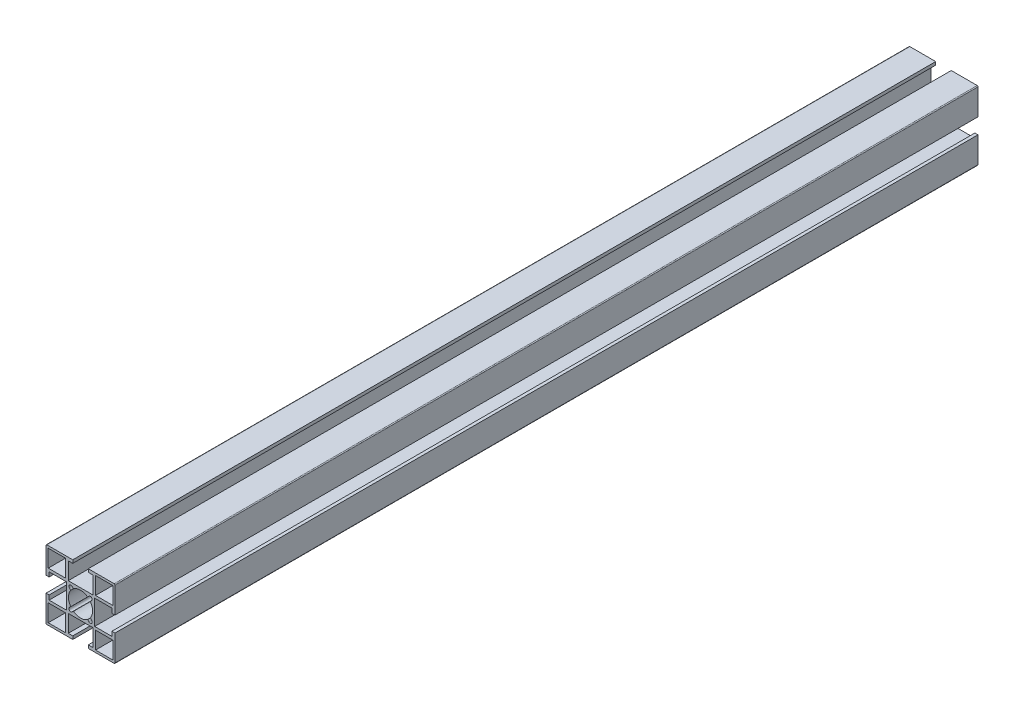
SolidWorks part; units mm, degrees
ref_plane "前视基准面" through (0, 0, 0) normal (0, 0, 1) x (1, 0, 0)
ref_plane "上视基准面" through (0, 0, 0) normal (0, 1, 0) x (1, 0, 0)
ref_plane "右视基准面" through (0, 0, 0) normal (1, 0, 0) x (0, 0, -1)
other "Configuration Table"
sketch "草图1" plane through (0, 0, 0) normal (1, 0, 0) x (0, 0, -1)
  line L0 (0, 0) -> (500, 0)
other "铝型材 40 X 40A X R0.5(1)"
ref_plane "基准面1" through (0, 0, 0) normal (0, 0, -1) x (0, 1, 0)
sketch "Sketch114" plane through (0, 0, 0) normal (0, 0, -1) x (0, 1, 0)
  line L0 (0, 0) -> (0, 16.3773) construction
  line L1 (0, 0) -> (-5.6569, 5.6569) construction
  line L2 (-19.5, 20) -> (-4.5, 20)
  line L3 (-20, 19.5) -> (-20, 4.5)
  line L4 (-19.5, -20) -> (-4.5, -20)
  line L5 (20, 19.5) -> (20, 4.5)
  line L6 (-4.879, 6.4347) -> (-4.1104, 5.6661)
  line L7 (-6.4347, 4.879) -> (-5.6661, 4.1104)
  line L8 (6.4347, 4.879) -> (5.6661, 4.1104)
  line L9 (0, 0) -> (20, 0) construction
  line L10 (4.879, 6.4347) -> (4.1104, 5.6661)
  line L11 (4.879, -6.4347) -> (4.1104, -5.6661)
  line L12 (6.4347, -4.879) -> (5.6661, -4.1104)
  line L13 (-6.4347, -4.879) -> (-5.6661, -4.1104)
  line L14 (-4.879, -6.4347) -> (-4.1104, -5.6661)
  line L15 (-4.5, 20) -> (-4.5, 18.2)
  line L16 (-18.7, 18.7) -> (-8.7, 18.7)
  line L17 (-18.7, 18.7) -> (-18.7, 8.7)
  line L18 (-18.7, 8.7) -> (-8.7, 8.7)
  line L19 (-8.7, 18.7) -> (-8.7, 8.7)
  line L20 (-7.1, 18.2) -> (-4.5, 18.2)
  line L21 (-7.1, 18.2) -> (-7.1, 8.2)
  line L22 (-7.1, 8.2) -> (7.1, 8.2)
  line L23 (7.1, 18.2) -> (7.1, 8.2)
  line L24 (4.5, 20) -> (4.5, 18.2)
  line L25 (4.5, 20) -> (19.5, 20)
  line L26 (4.5, 18.2) -> (7.1, 18.2)
  line L27 (8.7, 18.7) -> (8.7, 8.7)
  line L28 (18.7, 8.7) -> (8.7, 8.7)
  line L29 (18.7, 18.7) -> (18.7, 8.7)
  line L30 (18.7, 18.7) -> (8.7, 18.7)
  line L31 (18.2, 7.1) -> (8.2, 7.1)
  line L32 (18.2, 7.1) -> (18.2, 4.5)
  line L33 (20, 4.5) -> (18.2, 4.5)
  line L34 (8.2, 7.1) -> (8.2, -7.1)
  line L35 (18.2, -7.1) -> (8.2, -7.1)
  line L36 (18.2, -4.5) -> (18.2, -7.1)
  line L37 (20, -4.5) -> (18.2, -4.5)
  line L38 (7.1, -18.2) -> (7.1, -8.2)
  line L39 (7.1, -18.2) -> (4.5, -18.2)
  line L40 (4.5, -20) -> (4.5, -18.2)
  line L41 (7.1, -8.2) -> (-7.1, -8.2)
  line L42 (-7.1, -18.2) -> (-7.1, -8.2)
  line L43 (-4.5, -18.2) -> (-7.1, -18.2)
  line L44 (-4.5, -20) -> (-4.5, -18.2)
  line L45 (-18.2, -7.1) -> (-8.2, -7.1)
  line L46 (-18.2, -7.1) -> (-18.2, -4.5)
  line L47 (-20, -4.5) -> (-18.2, -4.5)
  line L48 (-8.2, -7.1) -> (-8.2, 7.1)
  line L49 (-18.2, 7.1) -> (-8.2, 7.1)
  line L50 (-18.2, 4.5) -> (-18.2, 7.1)
  line L51 (-20, 4.5) -> (-18.2, 4.5)
  line L52 (4.5, -20) -> (19.5, -20)
  line L53 (-20, -4.5) -> (-20, -19.5)
  line L54 (20, -4.5) -> (20, -19.5)
  line L55 (18.7, -18.7) -> (18.7, -8.7)
  line L56 (18.7, -8.7) -> (8.7, -8.7)
  line L57 (8.7, -18.7) -> (8.7, -8.7)
  line L58 (18.7, -18.7) -> (8.7, -18.7)
  line L59 (-8.7, -18.7) -> (-8.7, -8.7)
  line L60 (-18.7, -8.7) -> (-8.7, -8.7)
  line L61 (-18.7, -18.7) -> (-8.7, -18.7)
  line L62 (-18.7, -18.7) -> (-18.7, -8.7)
  arc A0 (-4.1104, 5.6661) -> (4.1104, 5.6661) centre (0, 0) cw
  arc A1 (-4.879, 6.4347) -> (-6.4347, 4.879) centre (-5.6569, 5.6569) ccw
  arc A2 (-4.1104, -5.6661) -> (4.1104, -5.6661) centre (0, 0) ccw
  arc A3 (-5.6661, 4.1104) -> (-5.6661, -4.1104) centre (0, 0) ccw
  arc A4 (6.4347, 4.879) -> (4.879, 6.4347) centre (5.6569, 5.6569) ccw
  arc A5 (4.879, -6.4347) -> (6.4347, -4.879) centre (5.6569, -5.6569) ccw
  arc A6 (-6.4347, -4.879) -> (-4.879, -6.4347) centre (-5.6569, -5.6569) ccw
  arc A7 (5.6661, 4.1104) -> (5.6661, -4.1104) centre (0, 0) cw
  arc A8 (-19.5, 20) -> (-20, 19.5) centre (-19.5, 19.5) ccw
  arc A9 (19.5, 20) -> (20, 19.5) centre (19.5, 19.5) cw
  arc A10 (19.5, -20) -> (20, -19.5) centre (19.5, -19.5) ccw
  arc A11 (-20, -19.5) -> (-19.5, -20) centre (-19.5, -19.5) ccw
  point P86 (20, 20)
  point P87 (-20, 20)
  point P88 (-20, -20)
  point P89 (20, -20)
  point P90 (0, 0)
  dimension "D2" = 7
  dimension "D3" = 45
  dimension "D4" = 1.1
  dimension "D5" = 1.8
  dimension "D6" = 8
  dimension "D7" = 1.3
  dimension "D8" = 14.2
  dimension "D10" = 10
  dimension "D11" = 10
  dimension "D12" = 40
  dimension "D13" = 9
  dimension "D14" = 0.5
  dimension "D9" = 1.3
